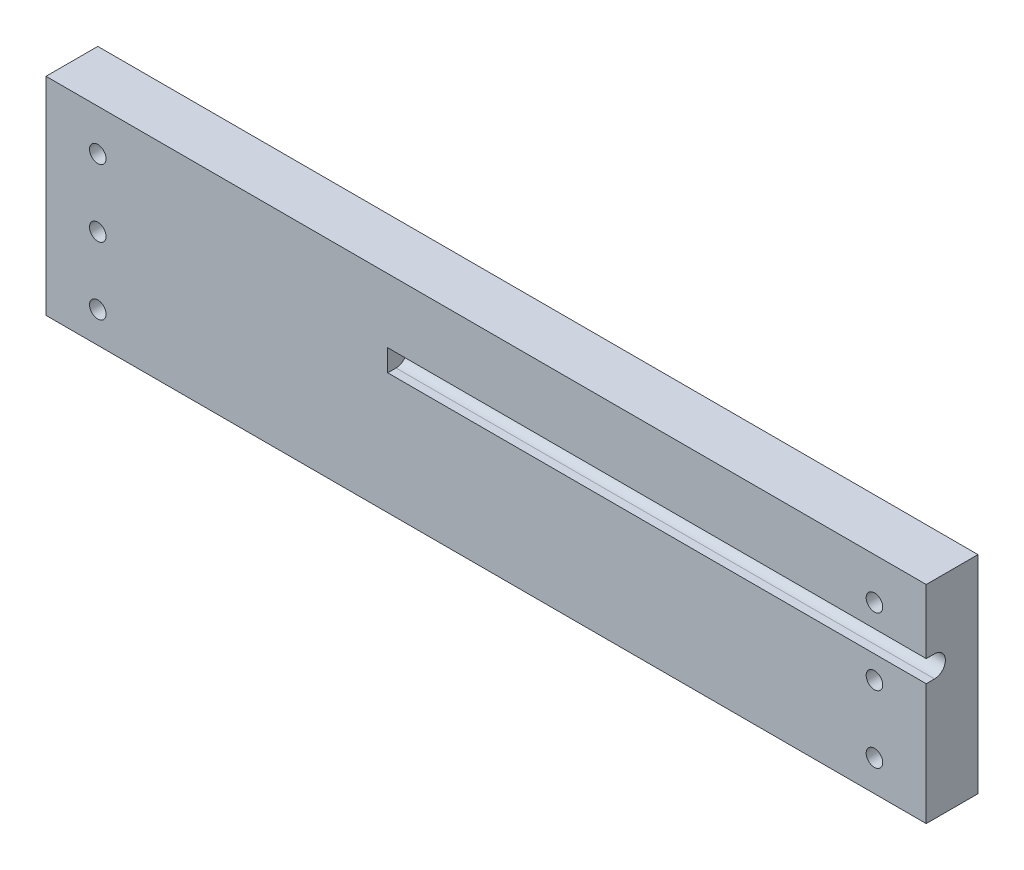
SolidWorks part; units mm, degrees
ref_plane "Front" through (0, 0, 0) normal (0, 0, 1) x (1, 0, 0)
ref_plane "Top" through (0, 0, 0) normal (0, 1, 0) x (1, 0, 0)
ref_plane "Right" through (0, 0, 0) normal (1, 0, 0) x (0, 0, -1)
sketch "Sketch1" plane through (0, 0, 0) normal (0, 0, 1) x (1, 0, 0)
  line L1 (-85, 40) -> (85, 40)
  line L2 (-85, 40) -> (-85, 0)
  line L3 (-85, 0) -> (85, 0)
  line L4 (85, 40) -> (85, 0)
  dimension "D1" = 170
  dimension "D2" = 40
extrude "Boss-Extrude1" add sketch "Sketch1" along normal blind 10
sketch "Sketch2" plane through (0, 0, 10) normal (0, 0, 1) x (1, 0, 0)
  line L1 (-85, 0) -> (85, 0) construction
  circle A0 centre (-75, 6) radius 1.6
  dimension "D1" = 3.2
  dimension "D2" = 75
  dimension "D3" = 6
extrude "Cut-M3 Hole" cut sketch "Sketch2" against normal through all
mirror "Mirror1" about plane through (0, 0, 0) normal (1, 0, 0) of "Cut-M3 Hole"
pattern_linear "LPattern1" count 3 spacing 13 along (0, 1, 0) of "Cut-M3 Hole", "Mirror1"
sketch "Sketch3" plane through (85, 0, 0) normal (1, 0, 0) x (0, 0, -1)
  line L0 (-10.5, 28.4774) -> (-10.5, 22.2555) construction
  line L1 (-10, 0) -> (-10, 40) construction
  line L2 (-8.4, 30.4) -> (-8.4, 20.6) construction
  line L3 (-10, 30.4) -> (0, 30.4) construction
  line L4 (0, 20.6) -> (-10, 20.6) construction
  circle A0 centre (-8.4, 25.5) radius 2.1
  dimension "D1" = 4.2
  dimension "D2" = 0.5
extrude "Cut-Tube Slot" cut sketch "Sketch3" against normal blind 104
sketch "Sketch4" plane through (85, 0, 0) normal (1, 0, 0) x (0, 0, -1)
  line L0 (-10, 26.8601) -> (-10, 40) construction
  line L1 (-10, 27.6) -> (-8.4, 27.6)
  line L2 (-10, 27.6) -> (-10, 23.4)
  line L3 (-10, 23.4) -> (-8.4, 23.4)
  line L4 (-8.4, 27.6) -> (-8.4, 23.4)
  arc A0 (-10, 24.1399) -> (-10, 26.8601) centre (-8.4, 25.5) ccw construction
  arc A1 (-10, 24.1399) -> (-10, 26.8601) centre (-8.4, 25.5) ccw construction
extrude "Cut-Extrude3" cut sketch "Sketch4" against normal up to surface (104 mm away) up to face at (-19, 25.5, 8.15)
